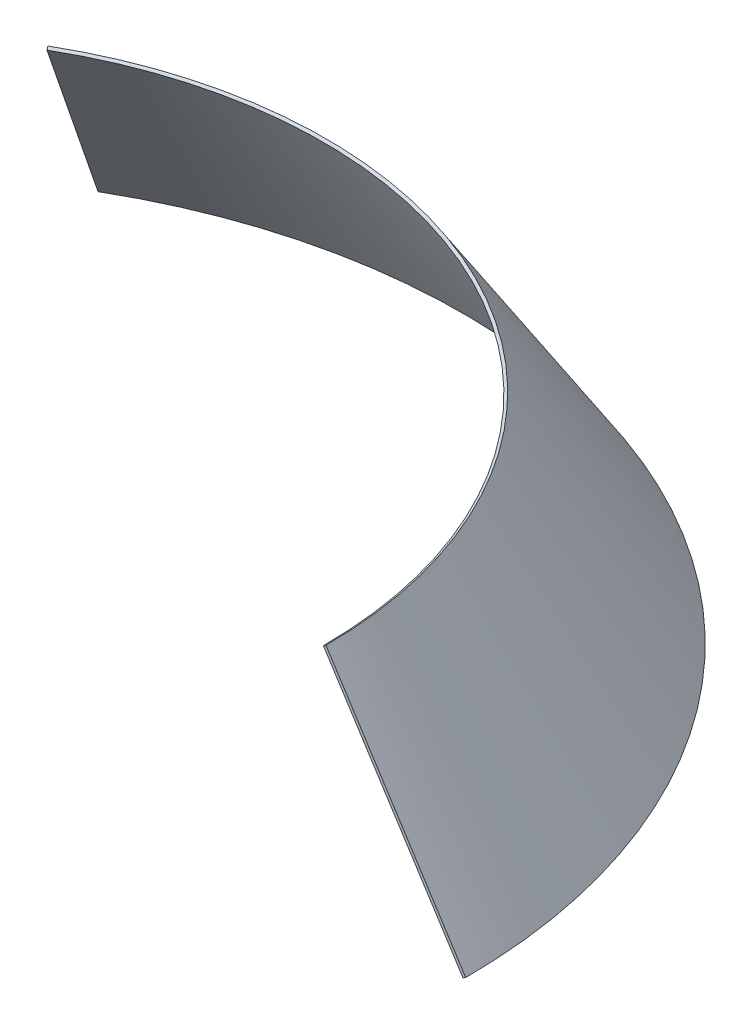
SolidWorks part; units mm, degrees
ref_plane "Přední rovina" through (0, 0, 0) normal (0, 0, 1) x (1, 0, 0)
ref_plane "Horní rovina" through (0, 0, 0) normal (0, 1, 0) x (1, 0, 0)
ref_plane "Pravá rovina" through (0, 0, 0) normal (1, 0, 0) x (0, 0, -1)
sketch "Skica6" plane through (0, 0, 0) normal (0, 0, 1) x (1, 0, 0)
  line L0 (90.5368, 0) -> (68.5705, 34.2853)
  line L1 (0, 0) -> (0, 52.3926) construction
revolve "Rotace tenkostěnný2" add sketch "Skica6" angle 120 about L1
